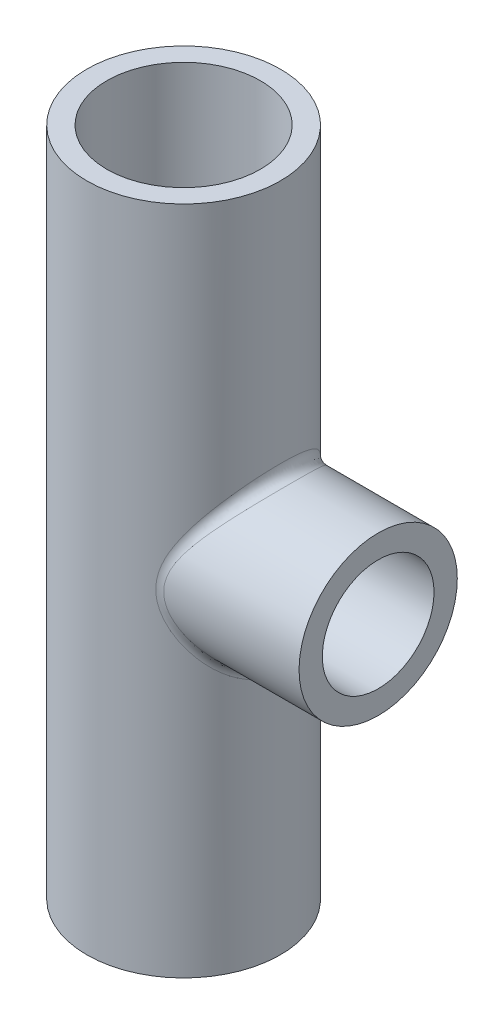
SolidWorks part; units mm, degrees
ref_plane "Front Plane" through (0, 0, 0) normal (0, 0, 1) x (1, 0, 0)
ref_plane "Top Plane" through (0, 0, 0) normal (0, 1, 0) x (1, 0, 0)
ref_plane "Right Plane" through (0, 0, 0) normal (1, 0, 0) x (0, 0, -1)
sketch "Sketch1" plane through (0, 0, 0) normal (0, 1, 0) x (1, 0, 0)
  circle A0 centre (0, 0) radius 10.4
  dimension "D1" = 20.8
extrude "Boss-Extrude1" add sketch "Sketch1" along normal blind 72
sketch "Sketch2" plane through (0, 0, 0) normal (1, 0, 0) x (0, 0, -1)
  line L0 (0, 72) -> (0, 0)
  line L1 (10.4, 72) -> (-10.4, 72) construction
  circle A0 centre (0, 36) radius 8.5
  dimension "D1" = 17
extrude "Boss-Extrude2" add sketch "Sketch2" along normal blind 20.9 contours A0
sketch "Sketch5" plane through (20.9, 0, 0) normal (1, 0, 0) x (0, 0, -1)
  circle A0 centre (0, 36) radius 6
  point P3 (0, 0)
  dimension "D1" = 12
extrude "Cut-Extrude1" cut sketch "Sketch5" against normal blind 20.9 contours A0
sketch "Sketch6" plane through (0, 72, 0) normal (0, 1, 0) x (1, 0, 0)
  circle A0 centre (0, 0) radius 8.25
  dimension "D1" = 16.5
extrude "Cut-Extrude2" cut sketch "Sketch6" against normal through all
fillet "Fillet1" radius 1.2 1 edges at (6.0169, 35.4585, -8.4827)
fillet "Fillet2" radius 1.2 1 edges at (5.6707, 36.3065, 5.9922)
